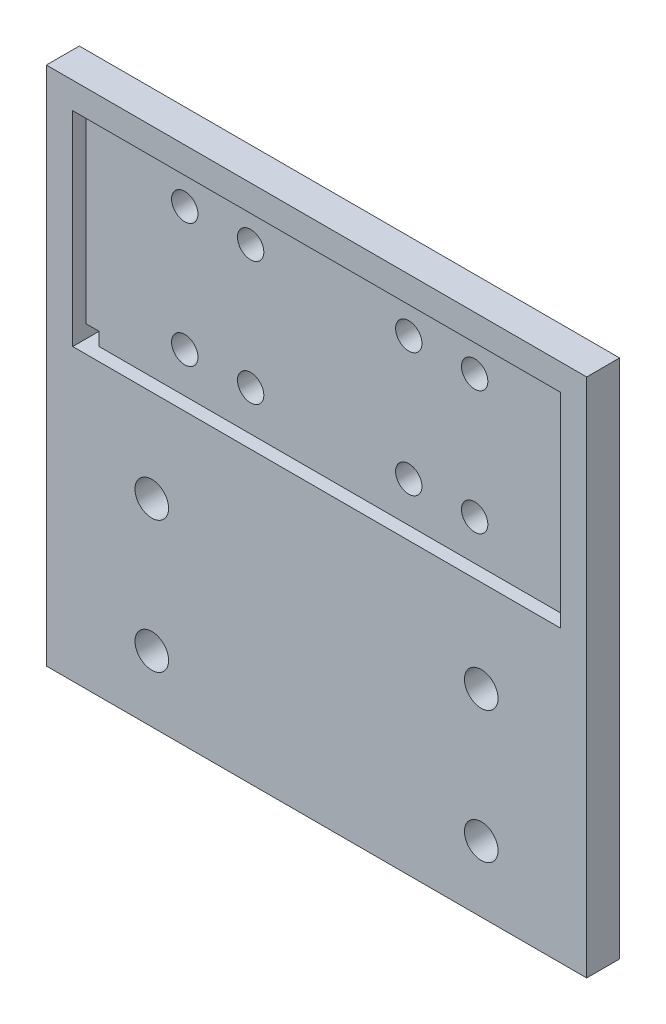
SolidWorks part; units mm, degrees
ref_plane "Front Plane" through (0, 0, 0) normal (0, 0, 1) x (1, 0, 0)
ref_plane "Top Plane" through (0, 0, 0) normal (0, 1, 0) x (1, 0, 0)
ref_plane "Right Plane" through (0, 0, 0) normal (1, 0, 0) x (0, 0, -1)
sketch "Sketch1" plane through (0, 0, 0) normal (0, 0, 1) x (1, 0, 0)
  line L0 (-41, -19.5) -> (-41, -59.5)
  line L1 (-36, -14.5) -> (36, -14.5) construction
  line L2 (-36, -14.5) -> (-36, 14.5) construction
  line L3 (-36, 14.5) -> (36, 14.5) construction
  line L4 (36, -14.5) -> (36, 14.5) construction
  line L5 (-36, -14.5) -> (36, 14.5) construction
  line L6 (-36, 14.5) -> (36, -14.5) construction
  line L7 (-41, -19.5) -> (41, -19.5) construction
  line L8 (-41, -19.5) -> (-41, 19.5)
  line L9 (-41, 19.5) -> (41, 19.5)
  line L10 (41, -19.5) -> (41, 19.5)
  line L11 (-41, -19.5) -> (41, 19.5) construction
  line L12 (-41, 19.5) -> (41, -19.5) construction
  line L13 (-41, -59.5) -> (41, -59.5)
  line L14 (41, -59.5) -> (41, -19.5)
  line L15 (0, 19.5) -> (0, -59.5) construction
  line L16 (-41, -29.5) -> (41, -29.5) construction
  line L17 (-41, -49.5) -> (41, -49.5) construction
  circle A0 centre (-25, -29.5) radius 2.55
  circle A1 centre (-25, -49.5) radius 2.55
  circle A2 centre (25, -49.5) radius 2.55
  circle A3 centre (25, -29.5) radius 2.55
  point P0 (0, 0)
  point P5 (0, 0)
  dimension "D6" = 5.1
  dimension "D7" = 5.1
  dimension "D8" = 25
  dimension "D9" = 25
  dimension "D1" = 29
  dimension "D2" = 72
  dimension "D3" = 5
  dimension "D4" = 5
  dimension "D5" = 40
  dimension "D10" = 10
  dimension "D11" = 30
extrude "Boss-Extrude1" add sketch "Sketch1" along normal blind 5 contours L9 L10 L14 L13 L0 L8
sketch "Sketch3" plane through (0, 0, 5) normal (0, 0, 1) x (1, 0, 0)
  line L32 (-37, -15.5) -> (37, -15.5)
  line L33 (37, -15.5) -> (37, 15.5)
  line L34 (37, 15.5) -> (-37, 15.5)
  line L35 (-37, 15.5) -> (-37, -15.5)
  line L36 (-37, -15.5) -> (37, -15.5)
  line L37 (37, -15.5) -> (37, 15.5)
  line L38 (37, 15.5) -> (-37, 15.5)
  line L39 (-37, 15.5) -> (-37, -15.5)
  circle A1 centre (25, -29.5) radius 2.55
  circle A2 centre (25, -29.5) radius 2.55
  circle A3 centre (25, -49.5) radius 2.55
  circle A4 centre (25, -49.5) radius 2.55
  circle A5 centre (-25, -49.5) radius 2.55
  circle A6 centre (-25, -49.5) radius 2.55
  circle A7 centre (-25, -29.5) radius 2.55
  circle A8 centre (-25, -29.5) radius 2.55
  point P0 (0, 0)
  dimension "D2" = 0
  dimension "D3" = 0
  dimension "D4" = 0
  dimension "D5" = 0
  dimension "D6" = 1
extrude "Cut-Extrude1" cut sketch "Sketch3" against normal blind 2
sketch "Sketch4" plane through (0, 0, 3) normal (0, 0, 1) x (1, 0, 0)
  line L0 (-37, 9.4) -> (37, 9.4) construction
  line L1 (-37, 15.5) -> (-37, -15.5) construction
  line L2 (37, -15.5) -> (37, 15.5) construction
  line L3 (37, 15.5) -> (-37, 15.5) construction
  line L4 (0, 15.5) -> (0, -15.5) construction
  line L5 (37, 15.5) -> (-37, 15.5) construction
  line L6 (-37, -15.5) -> (37, -15.5) construction
  line L7 (37, 0) -> (-37, 0) construction
  line L8 (37, -15.5) -> (37, 15.5) construction
  line L9 (-37, 15.5) -> (-37, -15.5) construction
  line L10 (-37, -15.5) -> (-37, -13.5)
  line L11 (-37, 15.5) -> (-35, 15.5)
  line L12 (-37, 15.5) -> (-37, 13.5)
  line L13 (-37, 13.5) -> (-35, 13.5)
  line L14 (-35, 15.5) -> (-35, 13.5)
  line L15 (-37, -15.5) -> (-35, -15.5)
  line L16 (-35, -15.5) -> (-35, -13.5)
  line L17 (-37, -13.5) -> (-35, -13.5)
  line L18 (37, 13.5) -> (35, 13.5)
  line L19 (37, 15.5) -> (37, 13.5)
  line L20 (37, 15.5) -> (35, 15.5)
  line L21 (35, 15.5) -> (35, 13.5)
  line L22 (37, -15.5) -> (35, -15.5)
  line L23 (37, -15.5) -> (37, -13.5)
  line L24 (37, -13.5) -> (35, -13.5)
  line L25 (35, -15.5) -> (35, -13.5)
  circle A0 centre (-22, 9.4) radius 2
  circle A1 centre (-12, 9.4) radius 2
  circle A2 centre (12, 9.4) radius 2
  circle A3 centre (22, 9.4) radius 2
  circle A4 centre (22, -9.4) radius 2
  circle A5 centre (12, -9.4) radius 2
  circle A6 centre (-12, -9.4) radius 2
  circle A7 centre (-22, -9.4) radius 2
  dimension "D2" = 10
  dimension "D4" = 4
  dimension "D5" = 4
  dimension "D1" = 6.1
  dimension "D3" = 24
  dimension "D6" = 2
  dimension "D7" = 2
extrude "Cut-Extrude2" cut sketch "Sketch4" against normal blind 5
